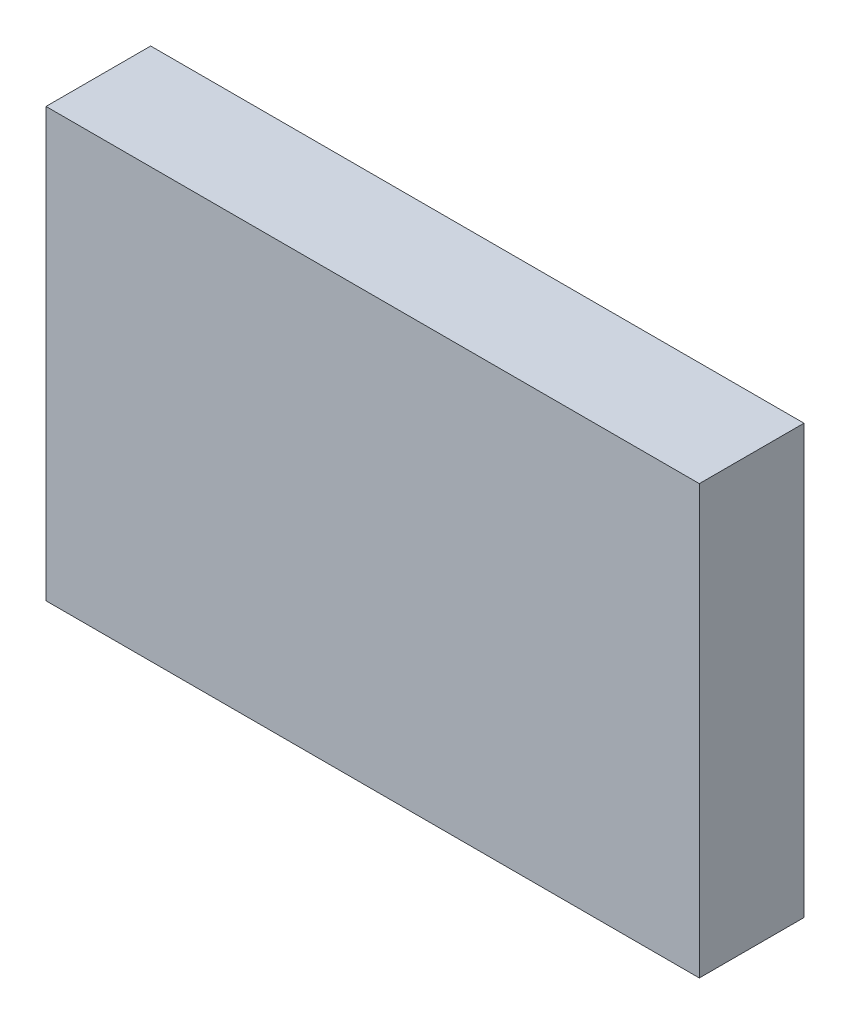
SolidWorks part; units mm, degrees
ref_plane "Front Plane" through (0, 0, 0) normal (0, 0, 1) x (1, 0, 0)
ref_plane "Top Plane" through (0, 0, 0) normal (0, 1, 0) x (1, 0, 0)
ref_plane "Right Plane" through (0, 0, 0) normal (1, 0, 0) x (0, 0, -1)
sketch "Sketch1" plane through (0, 0, 0) normal (0, 0, 1) x (1, 0, 0)
  line L1 (-103, 67.5) -> (103, 67.5)
  line L2 (-103, 67.5) -> (-103, -67.5)
  line L3 (-103, -67.5) -> (103, -67.5)
  line L4 (103, 67.5) -> (103, -67.5)
  line L5 (-103, 67.5) -> (103, -67.5) construction
  line L6 (-103, -67.5) -> (103, 67.5) construction
  point P0 (0, 0)
  dimension "D1" = 206
  dimension "D2" = 135
extrude "Boss-Extrude1" add sketch "Sketch1" along normal blind 33
sketch "Sketch2" plane through (-103, 0, 0) normal (-1, 0, 0) x (0, 0, 1)
  line L1 (22.5, -46) -> (7, -46)
  line L2 (22.5, -46) -> (22.5, -57.5)
  line L3 (22.5, -57.5) -> (7, -57.5)
  line L4 (7, -46) -> (7, -57.5)
  line L5 (22.5, -46) -> (7, -57.5) construction
  line L6 (22.5, -57.5) -> (7, -46) construction
  line L10 (33, 67.5) -> (0, 67.5) construction
  line L12 (33, 67.5) -> (33, -67.5) construction
  line L13 (33, -67.5) -> (0, -67.5) construction
  line L14 (0, 67.5) -> (0, -67.5) construction
  point P0 (14.75, -51.75)
  dimension "D1" = 10.5
  dimension "D2" = 7
  dimension "D3" = 113.5
  dimension "D4" = 10
extrude "Cut-Extrude1" cut sketch "Sketch2" against normal blind 100
sketch "Sketch3" plane through (-103, 0, 0) normal (-1, 0, 0) x (0, 0, 1)
  line L2 (33, 67.5) -> (33, -67.5) construction
  line L3 (33, -67.5) -> (0, -67.5) construction
  circle A0 centre (16.75, -15.25) radius 3.25
  point P2 (0, 0)
  dimension "D1" = 6.5
  dimension "D3" = 16.25
  dimension "D2" = 52.25
extrude "Cut-Extrude2" cut sketch "Sketch3" against normal blind 100
sketch "Sketch4" plane through (-103, 0, 0) normal (-1, 0, 0) x (0, 0, 1)
  line L2 (33, 67.5) -> (0, 67.5) construction
  line L3 (33, 67.5) -> (33, -67.5) construction
  circle A0 centre (16, 19) radius 8.5
  point P2 (0, 0)
  dimension "D1" = 48.5
  dimension "D2" = 17
  dimension "D3" = 17
extrude "Cut-Extrude3" cut sketch "Sketch4" against normal blind 100
